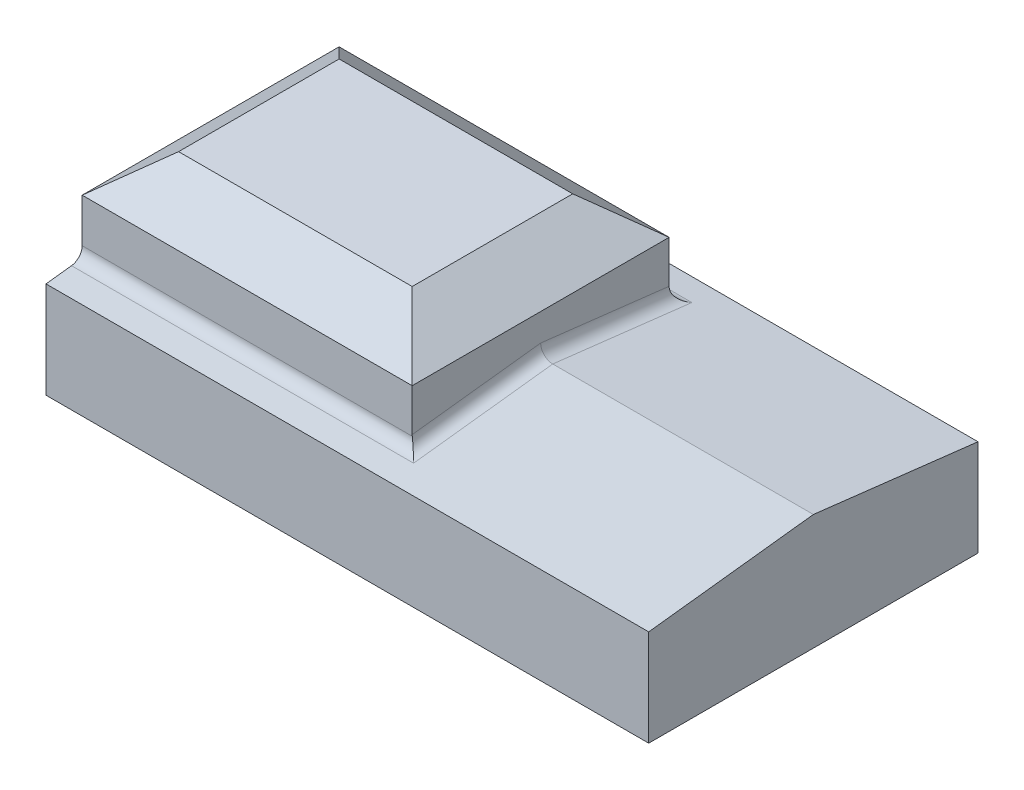
SolidWorks part; units mm, degrees
ref_plane "Front Plane" through (0, 0, 0) normal (0, 0, 1) x (1, 0, 0)
ref_plane "Top Plane" through (0, 0, 0) normal (0, 1, 0) x (1, 0, 0)
ref_plane "Right Plane" through (0, 0, 0) normal (1, 0, 0) x (0, 0, -1)
sketch "Croquis1" plane through (0, 0, 0) normal (1, 0, 0) x (0, 0, -1)
  line L0 (6.8291, 0) -> (-6.8291, 0)
  line L1 (-6.8291, 0) -> (-6.8291, 4)
  line L2 (6.8291, 0) -> (6.8291, 4)
  line L3 (6.8291, 4) -> (0, 4.8019)
  line L4 (0, 4.8019) -> (-6.8291, 4)
  point P3 (0, 0)
  point P4 (0, 0)
  point P7 (0, 0)
  point P9 (-7.6165, 0)
  point P10 (0, 0)
  point P11 (-8.0887, 10)
  point P12 (8.1191, 0)
  point P13 (0, 4.9789)
  point P14 (-7.9516, 10)
  point P15 (0, 5.6187)
  point P16 (0, 5.8168)
  point P17 (0, 4.9337)
  point P18 (6.8291, 0)
  dimension "D1" = 4
extrude "Saliente-Extruir1" add sketch "Croquis1" along normal blind 25
sketch "Croquis2" plane through (0, 0, 0) normal (0, 1, 0) x (1, 0, 0)
  line L0 (0, 6.8291) -> (0, 0) construction
  line L1 (0, 5.3291) -> (13.6891, 5.3291)
  line L2 (0, 5.3291) -> (0, -5.3291)
  line L3 (0, -5.3291) -> (13.6891, -5.3291)
  line L4 (13.6891, 5.3291) -> (13.6891, -5.3291)
  line L5 (25, 6.8291) -> (0, 6.8291) construction
  line L6 (5.0615, 5.3291) -> (5.0615, 6.8291) construction
  line L7 (5.0615, -5.3291) -> (5.0615, -6.8291) construction
  line L8 (25, -6.8291) -> (0, -6.8291) construction
  dimension "D1" = 1.5
extrude "Saliente-Extruir2" add sketch "Croquis2" along normal blind 8
fillet "Redondeo1" radius 0.5 4 edges at (6.8446, 4.1761, -5.3291) (13.6891, 4.489, -2.6646) (13.6891, 4.489, 2.6646) (6.8446, 4.1761, 5.3291)
chamfer "Chaflán2" distance 2 angle 38 4 edges at (0, 8, 0) (6.8446, 8, -5.3291) (13.6891, 8, 0) (6.8446, 8, 5.3291)
scale "Escala2" scale about centroid uniform scaling yes scale factor 1.5
scale "Escala3" scale about centroid uniform scaling yes scale factor 1.01
scale "Escala4" scale about centroid uniform scaling yes scale factor 1.01
scale "Escala5" scale about centroid uniform scaling yes scale factor 1.01
